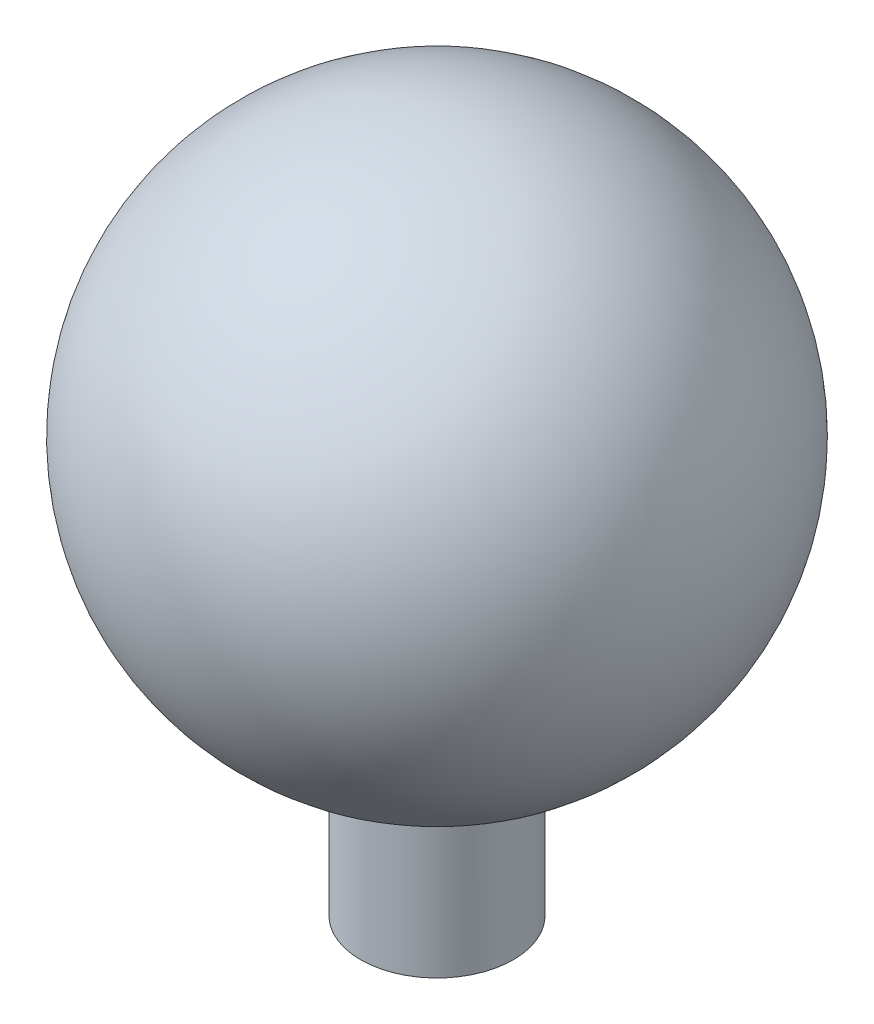
SolidWorks part; units mm, degrees
ref_plane "Front Plane" through (0, 0, 0) normal (0, 0, 1) x (1, 0, 0)
ref_plane "Top Plane" through (0, 0, 0) normal (0, 1, 0) x (1, 0, 0)
ref_plane "Right Plane" through (0, 0, 0) normal (1, 0, 0) x (0, 0, -1)
sketch "Sketch1" plane through (0, 0, 0) normal (0, 0, 1) x (1, 0, 0)
  line L0 (0, 79.5) -> (0, -79.5)
  line L1 (0, -79.5) -> (0, -119.5)
  line L2 (0, -119.5) -> (22, -119.5)
  line L3 (22, -119.5) -> (22, -76.3954)
  arc A0 (0, 79.5) -> (22, -76.3954) centre (0, 0) cw
  point P3 (0, 0)
  dimension "D1" = 79.5
  dimension "D2" = 22
  dimension "D3" = 119.5
revolve "Revolve1" add sketch "Sketch1" angle 360 about L0
